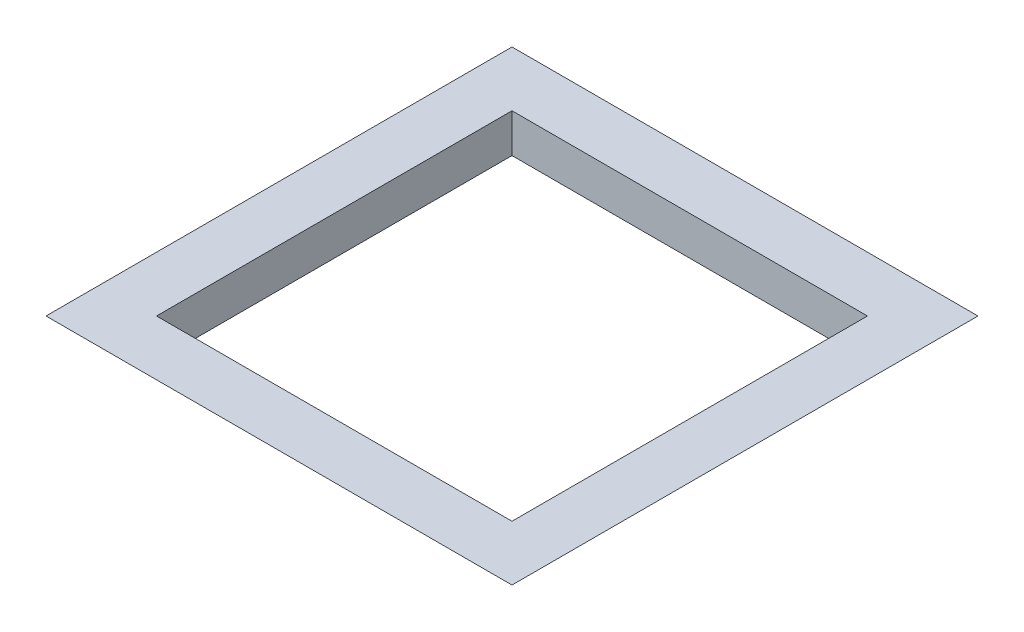
SolidWorks part; units mm, degrees
ref_plane "Front Plane" through (0, 0, 0) normal (0, 0, 1) x (1, 0, 0)
ref_plane "Top Plane" through (0, 0, 0) normal (0, 1, 0) x (1, 0, 0)
ref_plane "Right Plane" through (0, 0, 0) normal (1, 0, 0) x (0, 0, -1)
sketch "Sketch1" plane through (0, 0, 0) normal (0, 1, 0) x (1, 0, 0)
  line L1 (0, 0) -> (130, 0)
  line L2 (0, 0) -> (0, 130)
  line L3 (0, 130) -> (130, 130)
  line L4 (130, 0) -> (130, 130)
extrude "Boss-Extrude1" add sketch "Sketch1" along normal blind 13 draft 45 draft outward yes
sketch "Sketch2" plane through (0, 13, 0) normal (0, 1, 0) x (1, 0, 0)
  line L0 (-13, 65) -> (143, 65) construction
  line L1 (-13, 143) -> (-13, -13) construction
  line L2 (143, -13) -> (143, 143) construction
  line L3 (5.5, 23.7215) -> (-13, 23.7215) construction
  line L4 (-13, -13) -> (143, -13) construction
  line L5 (65, 143) -> (65, -13) construction
  line L6 (143, 143) -> (-13, 143) construction
  line L7 (5.5, 124.5) -> (124.5, 124.5)
  line L8 (5.5, 124.5) -> (5.5, 5.5)
  line L9 (5.5, 5.5) -> (124.5, 5.5)
  line L10 (124.5, 124.5) -> (124.5, 5.5)
  line L11 (124.5, 22.2798) -> (143, 22.2798) construction
  line L12 (27.0447, 124.5) -> (27.0447, 143) construction
  line L13 (27.0447, 5.5) -> (27.0447, -13) construction
extrude "Cut-Extrude1" cut sketch "Sketch2" against normal blind 13
